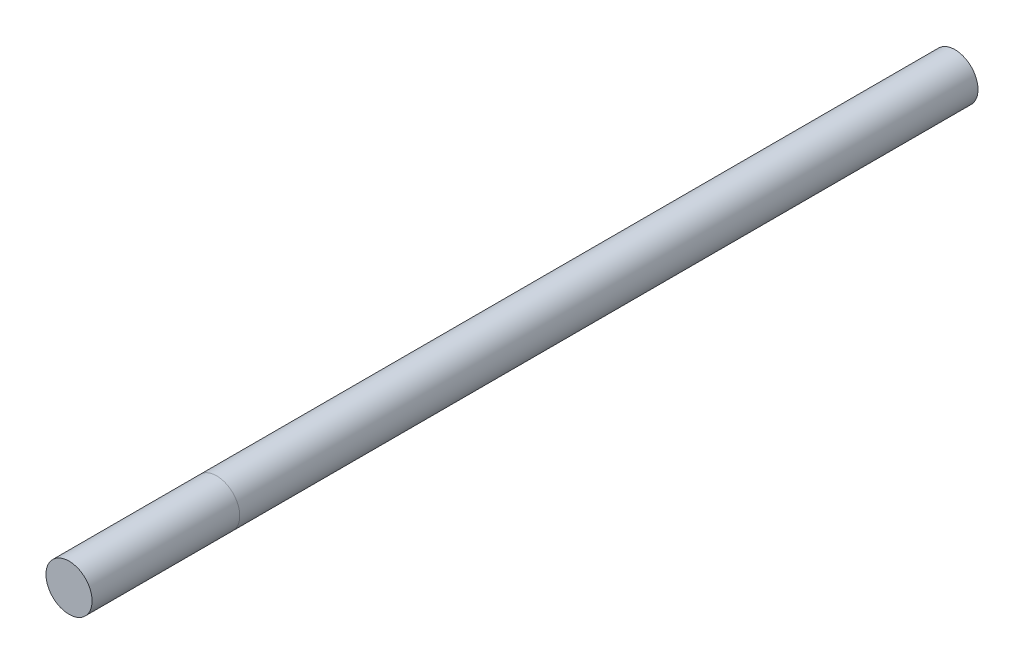
SolidWorks part; units mm, degrees
ref_plane "前视基准面" through (0, 0, 0) normal (0, 0, 1) x (1, 0, 0)
ref_plane "上视基准面" through (0, 0, 0) normal (0, 1, 0) x (1, 0, 0)
ref_plane "右视基准面" through (0, 0, 0) normal (1, 0, 0) x (0, 0, -1)
sketch "草图1" plane through (0, 0, 0) normal (0, 0, 1) x (1, 0, 0)
  circle A0 centre (0, 0) radius 2.5
  dimension "D1" = 5
extrude "凸台-拉伸1" add sketch "草图1" along normal blind 80
sketch "草图2" plane through (0, 0, 80) normal (0, 0, 1) x (1, 0, 0)
  circle A0 centre (0, 0) radius 2.5
  dimension "D1" = 5
extrude "凸台-拉伸2" add sketch "草图2" along normal blind 16
cosmetic thread "装饰螺纹线1" parameters "D2"=4
